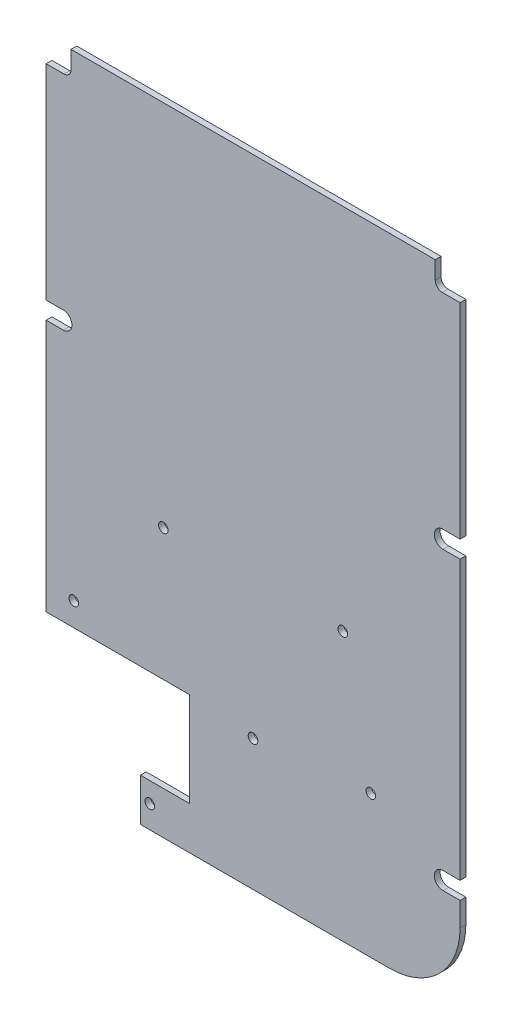
SolidWorks part; units mm, degrees
ref_plane "前视基准面" through (0, 0, 0) normal (0, 0, 1) x (1, 0, 0)
ref_plane "上视基准面" through (0, 0, 0) normal (0, 1, 0) x (1, 0, 0)
ref_plane "右视基准面" through (0, 0, 0) normal (1, 0, 0) x (0, 0, -1)
sketch "草图1" plane through (0, 0, 0) normal (0, 0, 1) x (1, 0, 0)
  line L0 (44.125, 15.2) -> (44.125, -44.1)
  line L1 (-44.125, 67.85) -> (44.125, 67.85)
  line L2 (-44.125, 67.85) -> (-44.125, 18.9)
  line L3 (-24.025, -67.85) -> (29.125, -67.85)
  line L4 (44.125, 67.85) -> (44.125, 18.9)
  line L5 (-44.125, 67.85) -> (44.125, -67.85) construction
  line L6 (-44.125, -67.85) -> (44.125, 67.85) construction
  line L7 (40.475, 18.9) -> (44.125, 18.9)
  line L9 (40.475, 15.2) -> (44.125, 15.2)
  line L11 (40.475, -44.1) -> (44.125, -44.1)
  line L13 (40.475, -47.8) -> (44.125, -47.8)
  line L15 (44.125, -47.8) -> (44.125, -52.85)
  line L17 (-44.125, -38.65) -> (-13.525, -38.65)
  line L20 (-13.525, -38.65) -> (-13.525, -58.75)
  line L21 (-24.025, -58.75) -> (-24.025, -67.85)
  line L22 (-24.025, -58.75) -> (-13.525, -58.75)
  line L23 (-44.125, 15.2) -> (-44.125, -38.65)
  line L24 (-40.475, 18.9) -> (-44.125, 18.9)
  line L26 (-40.475, 15.2) -> (-44.125, 15.2)
  arc A0 (29.125, -67.85) -> (44.125, -52.85) centre (29.125, -52.85) ccw
  arc A1 (40.475, 18.9) -> (40.475, 15.2) centre (40.475, 17.05) ccw
  arc A2 (40.475, -44.1) -> (40.475, -47.8) centre (40.475, -45.95) ccw
  circle A3 centre (-22.025, -63) radius 1.025
  arc A4 (-40.475, 15.2) -> (-40.475, 18.9) centre (-40.475, 17.05) ccw
  circle A5 centre (-19.125, -10.6) radius 1.025
  circle A6 centre (-0.025, -39.95) radius 1.025
  circle A7 centre (-38.225, -33.65) radius 1.025
  circle A8 centre (25.075, -37.55) radius 1.025
  circle A9 centre (19.125, -10.6) radius 1.025
  point P0 (0, 0)
  dimension "D3" = 15
  dimension "D4" = 1.85
  dimension "D5" = 1.85
  dimension "D18" = 4.85
  dimension "D19" = 2.05
  dimension "D21" = 3.7
  dimension "D24" = 2.05
  dimension "D25" = 2.05
  dimension "D26" = 2.05
  dimension "D27" = 2.05
  dimension "D28" = 2.05
  dimension "D36" = 13.5
  dimension "D1" = 135.7
  dimension "D2" = 88.25
  dimension "D6" = 3.65
  dimension "D7" = 3.65
  dimension "D8" = 50.8
  dimension "D9" = 3.7
  dimension "D10" = 113.8
  dimension "D11" = 3.7
  dimension "D12" = 106.5
  dimension "D13" = 88.25
  dimension "D14" = 30.6
  dimension "D15" = 10.5
  dimension "D16" = 135.7
  dimension "D17" = 9.1
  dimension "D20" = 2
  dimension "D22" = 3.65
  dimension "D23" = 0
  dimension "D29" = 25
  dimension "D30" = 57.25
  dimension "D31" = 25
  dimension "D32" = 57.25
  dimension "D33" = 5.9
  dimension "D34" = 5
  dimension "D35" = 27.9
  dimension "D37" = 19.05
  dimension "D38" = 30.3
extrude "凸台-拉伸1" add sketch "草图1" along normal blind 1.23
sketch "草图2" plane through (0, 0, 1.23) normal (0, 0, 1) x (1, 0, 0)
  line L1 (-44.125, 67.85) -> (-38.825, 67.85)
  line L2 (-44.125, 67.85) -> (-44.125, 62.55)
  line L3 (-44.125, 62.55) -> (-38.825, 62.55)
  line L4 (-38.825, 67.85) -> (-38.825, 62.55)
  line L5 (44.125, 67.85) -> (38.825, 67.85)
  line L6 (44.125, 67.85) -> (44.125, 62.55)
  line L7 (44.125, 62.55) -> (38.825, 62.55)
  line L8 (38.825, 67.85) -> (38.825, 62.55)
  dimension "D1" = 5.3
  dimension "D2" = 5.3
  dimension "D3" = 5.3
  dimension "D4" = 5.3
extrude "切除-拉伸1" cut sketch "草图2" against normal blind 10
fillet "圆角1" radius 1.5 2 edges at (38.825, 62.55, 0.615) (-38.825, 62.55, 0.615)
